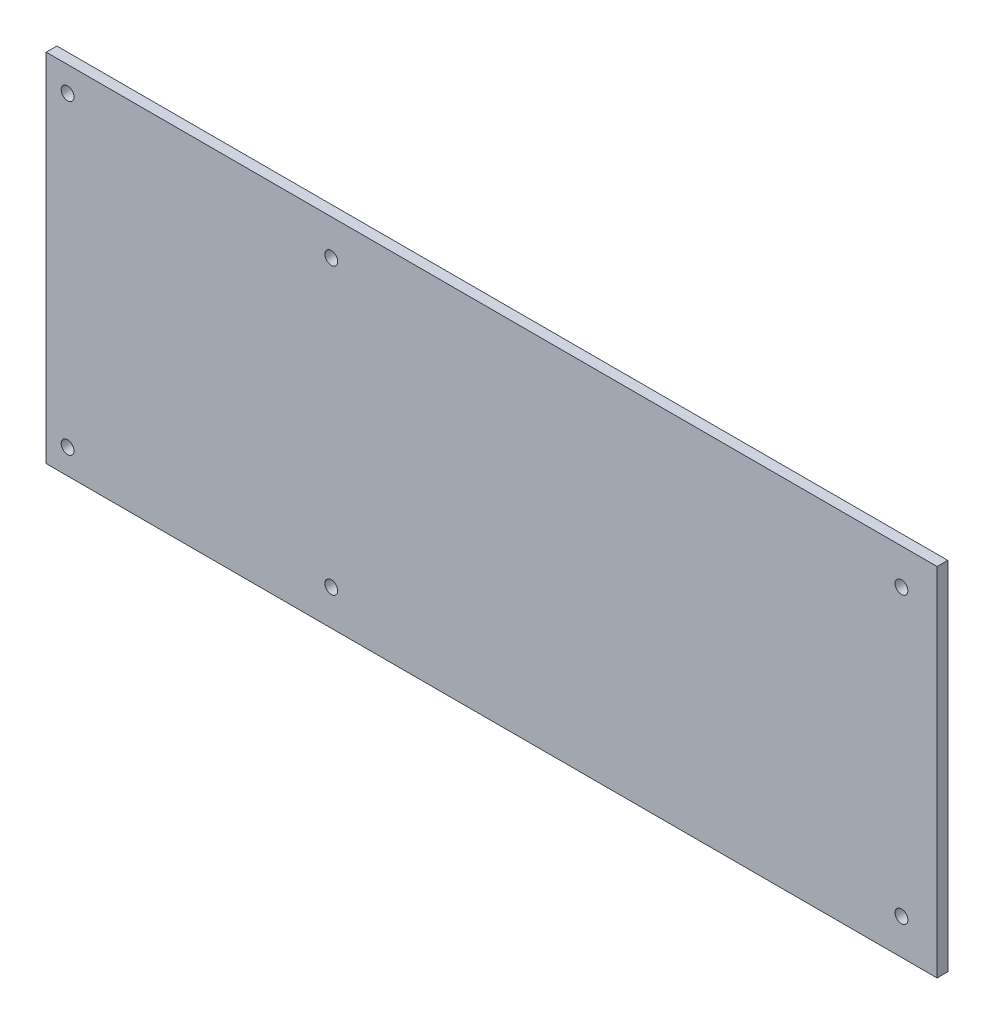
SolidWorks part; units mm, degrees
material "PMMA laser cult panels"
ref_plane "Front Plane" through (0, 0, 0) normal (0, 0, 1) x (1, 0, 0)
ref_plane "Top Plane" through (0, 0, 0) normal (0, 1, 0) x (1, 0, 0)
ref_plane "Right Plane" through (0, 0, 0) normal (1, 0, 0) x (0, 0, -1)
sketch "Sketch1" plane through (0, 0, 0) normal (0, 0, 1) x (1, 0, 0)
  line L1 (0, 0) -> (250, 0)
  line L2 (0, 0) -> (0, 100)
  line L3 (0, 100) -> (250, 100)
  line L4 (250, 0) -> (250, 100)
  dimension "D1" = 250
  dimension "D2" = 100
extrude "Boss-Extrude1" add sketch "Sketch1" along normal blind 3
sketch "Sketch2" plane through (0, 0, 3) normal (0, 0, 1) x (1, 0, 0)
  line L0 (0, 0) -> (250, 0) construction
  line L1 (250, 100) -> (0, 100) construction
  line L2 (0, 100) -> (0, 0) construction
  circle A0 centre (6, 93) radius 1.8
  circle A1 centre (80, 90) radius 1.8
  circle A2 centre (240, 90) radius 1.8
  circle A3 centre (240, 10) radius 1.8
  circle A4 centre (80, 10) radius 1.8
  circle A5 centre (6, 7) radius 1.8
  dimension "D6" = 10
  dimension "D7" = 10
  dimension "D8" = 3.6
  dimension "D1" = 7
  dimension "D2" = 7
  dimension "D3" = 6
  dimension "D4" = 80
  dimension "D5" = 240
extrude "Cut-Extrude1" cut sketch "Sketch2" against normal through all
